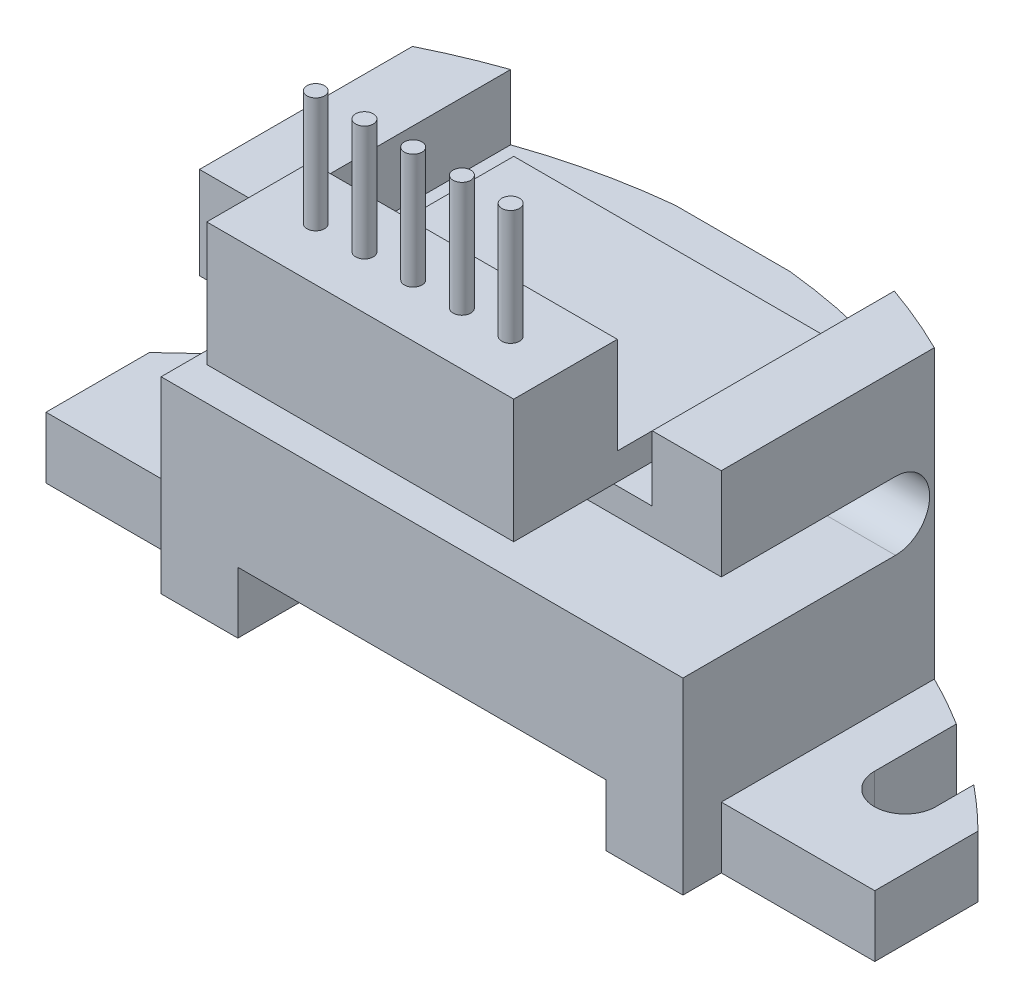
SolidWorks part; units mm, degrees
ref_plane "Front Plane" through (0, 0, 0) normal (0, 0, 1) x (1, 0, 0)
ref_plane "Top Plane" through (0, 0, 0) normal (0, 1, 0) x (1, 0, 0)
ref_plane "Right Plane" through (0, 0, 0) normal (1, 0, 0) x (0, 0, -1)
sketch "Sketch1" plane through (0, 0, 0) normal (0, 1, 0) x (1, 0, 0)
  line L0 (0, 0) -> (8.9, 0) construction
  line L1 (10.8, 0) -> (10.8, -2.69)
  line L2 (0, 0) -> (0, 4.4) construction
  line L3 (0, 4.4) -> (1.5, 4.4) construction
  line L4 (0, -2.69) -> (6.8, -2.69) construction
  line L5 (6.8, -2.69) -> (10.8, -2.69)
  line L6 (6.8, -2.69) -> (6.8, 2.861)
  line L7 (8.1, 0) -> (8.1, 2.1345)
  line L8 (9.7, 0) -> (9.7, 0.9893)
  arc A0 (1.5, 4.4) -> (8.1, 2.1345) centre (-0.1031, -11.0169) cw construction
  circle A1 centre (8.9, 0) radius 0.8 construction
  arc A2 (9.7, 0.9893) -> (10.8, 0) centre (-0.1031, -11.0169) cw
  arc A3 (8.1, 2.1345) -> (6.8, 2.861) centre (-0.1031, -11.0169) ccw
  arc A4 (9.7, 0) -> (8.1, 0) centre (8.9, 0) cw
  dimension "D7" = 15.5
  dimension "D8" = 1.6
  dimension "D1" = 8.9
  dimension "D2" = 10.8
  dimension "D3" = 2.69
  dimension "D4" = 4.4
  dimension "D5" = 1.5
  dimension "D6" = 6.8
extrude "Boss-Extrude1" add sketch "Sketch1" along normal blind 1.6 contours L8 A4 L7 A3 L6 L5 L1 A2
sketch "Sketch2" plane through (0, 1.6, 0) normal (0, 1, 0) x (1, 0, 0)
  line L0 (6.8, -2.69) -> (6.8, 2.861) construction
  line L1 (6.8, -2.69) -> (6.8, 2.861)
  line L2 (6.8, -2.69) -> (4.8, -2.69)
  line L3 (0, -2.69) -> (6.8, -2.69) construction
  line L4 (4.8, -2.69) -> (4.8, 3.6872)
  arc A0 (8.1, 2.1345) -> (1.5, 4.4) centre (-0.1031, -11.0169) ccw construction
  arc A1 (4.8, 3.6872) -> (6.8, 2.861) centre (-0.1031, -11.0169) cw
  dimension "D1" = 2
extrude "Boss-Extrude2" add sketch "Sketch2" against normal blind 1.6
sketch "Sketch3" plane through (0, 1.6, 0) normal (0, 1, 0) x (1, 0, 0)
  line L0 (6.8, -2.69) -> (6.8, 2.861) construction
  line L1 (6.8, -2.69) -> (6.8, 2.861)
  line L2 (0, -2.69) -> (6.8, -2.69)
  line L3 (1.5, 4.4) -> (1.5, 1.9)
  line L4 (1.5, 1.9) -> (0, 1.9)
  line L5 (0, 0) -> (0, 4.4) construction
  line L6 (0, 1.9) -> (0, -2.69) construction
  line L7 (0, 1.9) -> (0, -2.69)
  arc A0 (8.1, 2.1345) -> (1.5, 4.4) centre (-0.1031, -11.0169) ccw construction
  arc A1 (6.8, 2.861) -> (1.5, 4.4) centre (-0.1031, -11.0169) ccw
  dimension "D1" = 2.5
extrude "Boss-Extrude3" add sketch "Sketch3" along normal blind 3.3
sketch "Sketch4" plane through (0, 0, 2.69) normal (0, 0, 1) x (1, 0, 0)
  line L0 (6.8, 1.6) -> (6.8, 0)
  line L1 (8.1, 0) -> (6.8, 0) construction
  line L2 (8.1, 0) -> (1.5, 0) construction
  line L3 (6.8, 4.9) -> (6.8, 1.6) construction
  line L4 (4.8, 0) -> (4.8, 1.6) construction
  line L5 (6.8, 4.9) -> (6.8, 1.6)
  line L6 (4.8, 0) -> (4.8, 1.6)
  line L7 (4.8, 0) -> (6.8, 0)
  line L12 (0, 4.9) -> (6.8, 4.9)
  line L13 (0, 4.9) -> (0, 1.6) construction
  line L14 (0, 4.9) -> (6.8, 4.9) construction
  line L15 (0, 4.9) -> (0, 1.6)
  line L16 (0, 1.6) -> (4.8, 1.6)
extrude "Boss-Extrude4" add sketch "Sketch4" along normal blind 1
sketch "Sketch5" plane through (0, 0, 0) normal (-1, 0, 0) x (0, 0, 1)
  line L0 (0, 0) -> (0, 4.9) construction
  line L1 (-1.9, 4.9) -> (3.69, 4.9) construction
  line L2 (0, 4.9) -> (0, 6.68) construction
  line L3 (0, 6.68) -> (11, 6.68) construction
  line L4 (11, 6.18) -> (-1.85, 6.18) construction
  line L5 (0, 5.79) -> (-1.85, 5.79) construction
  line L6 (-4.4, 4.9) -> (-1.9, 4.9) construction
  line L7 (-1.85, 5.79) -> (-1.85, 4.9) construction
  line L8 (-2.861, 4.9) -> (-1.85, 4.9)
  line L9 (2.69, 0) -> (2.69, 1.6) construction
  line L10 (2.69, 0) -> (2.69, 1.6) construction
  line L11 (-1.85, 6.68) -> (2.69, 6.68)
  line L12 (2.69, 6.68) -> (2.69, 9.08)
  line L13 (2.69, 9.08) -> (-2.861, 9.08)
  line L14 (-2.861, 4.9) -> (-2.861, 1.6) construction
  line L15 (-2.861, 4.9) -> (-2.861, 1.6) construction
  line L16 (-2.861, 9.08) -> (-2.861, 4.9)
  circle A0 centre (-1.85, 5.79) radius 0.89 construction
  arc A1 (-1.85, 4.9) -> (-1.85, 6.68) centre (-1.85, 5.79) cw
  dimension "D1" = 1.78
  dimension "D2" = 11
  dimension "D3" = 0.5
  dimension "D4" = 12.85
  dimension "D5" = 2.4
sketch "Sketch6" plane through (6.8, 0, 0) normal (1, 0, 0) x (0, 0, -1)
  line L0 (-2.69, 9.08) -> (2.861, 9.08) construction
  line L1 (-2.69, 6.68) -> (-2.69, 9.08) construction
  line L2 (1.85, 6.68) -> (-2.69, 6.68) construction
  line L3 (2.861, 4.9) -> (1.85, 4.9) construction
  line L4 (2.861, 9.08) -> (2.861, 4.9) construction
  line L5 (-2.69, 9.08) -> (2.861, 9.08)
  line L6 (-2.69, 6.68) -> (-2.69, 9.08)
  line L7 (1.85, 6.68) -> (-2.69, 6.68)
  line L8 (2.861, 4.9) -> (1.85, 4.9)
  line L9 (2.861, 9.08) -> (2.861, 4.9)
  arc A0 (1.85, 4.9) -> (1.85, 6.68) centre (1.85, 5.79) ccw construction
  arc A1 (1.85, 4.9) -> (1.85, 6.68) centre (1.85, 5.79) ccw
extrude "Boss-Extrude5" add sketch "Sketch6" against normal up to surface (6.8 mm away) up to face at (0, 3.25, 0.895)
sketch "Sketch7" plane through (0, 4.9, 0) normal (0, 1, 0) x (1, 0, 0)
  line L0 (0, 2.861) -> (6.8, 2.861) construction
  line L1 (0, 4.4) -> (1.5, 4.4) construction
  line L2 (0, 2.861) -> (6.8, 2.861)
  line L3 (0, 4.4) -> (1.5, 4.4)
  line L4 (0, 4.4) -> (0, 2.861)
  arc A0 (8.1, 2.1345) -> (1.5, 4.4) centre (-0.1031, -11.0169) ccw construction
  arc A1 (8.1, 2.1345) -> (1.5, 4.4) centre (-0.1031, -11.0169) ccw
  line M1 (1.5, 2.861) -> (6.8, 2.861)
  arc M2 (6.8, 2.861) -> (1.5, 4.4) centre (-0.1031, -11.0169) ccw
  line M3 (1.5, 4.4) -> (1.5, 2.861)
extrude "Boss-Extrude6" add sketch "Sketch7" along normal up to surface (4.18 mm away) contours L3 L4 L2 M3 | M3 M1 M2 up to face at (3.4, 9.08, -0.0855)
sketch "Sketch8" plane through (0, 0, 0) normal (0, -1, 0) x (1, 0, 0)
  circle A0 centre (6.3, 0) radius 1
  dimension "D2" = 2
  dimension "D1" = 6.3
extrude "Boss-Extrude7" add sketch "Sketch8" along normal blind 0.8
sketch "Sketch9" plane through (0, 0, 2.69) normal (0, 0, 1) x (1, 0, 0)
  line L1 (0, 9.08) -> (5, 9.08)
  line L2 (0, 9.08) -> (0, 7.38)
  line L3 (0, 7.38) -> (5, 7.38)
  line L4 (5, 9.08) -> (5, 7.38)
  dimension "D1" = 5
  dimension "D2" = 1.7
extrude "Cut-Extrude1" cut sketch "Sketch9" against normal through all
mirror "Mirror3" about plane through (0, 4.9, -1.9) normal (1, 0, 0) of bodies 110
sketch "Sketch10" plane through (0, 0, 0) normal (1, 0, 0) x (0, 0, -1)
  line L0 (0, 0) -> (0, 7.38) construction
  line L1 (-1, 0) -> (1, 0) construction
  line L3 (3.619, 7.38) -> (-2.69, 7.38) construction
  line L4 (3.619, 7.38) -> (-2.69, 7.38) construction
  line L5 (0, 7.38) -> (-5.3, 7.38)
  line L6 (-5.3, 7.38) -> (-5.3, 10.6)
  line L7 (-5.3, 10.6) -> (-2.6, 10.6)
  line L8 (-2.6, 10.6) -> (-2.6, 8.08)
  line L9 (-2.6, 8.08) -> (0, 8.08)
  line L10 (0, 8.08) -> (0, 7.38) construction
  line L11 (0, 8.08) -> (2.7, 8.08)
  line L12 (2.7, 8.08) -> (2.7, 7.38)
  line L13 (2.7, 7.38) -> (0, 7.38)
  line L14 (2.861, 9.08) -> (-2.69, 9.08) construction
  dimension "D1" = 5.3
  dimension "D2" = 1.52
  dimension "D3" = 0.7
  dimension "D4" = 2.7
  dimension "D5" = 2.7
extrude "Boss-Extrude8" add sketch "Sketch10" along normal mid plane 8
sketch "Sketch11" plane through (0, 0, 0) normal (1, 0, 0) x (0, 0, -1)
  line L0 (-3.69, 10.6) -> (-3.69, 11.9743) construction
  line L1 (-2.6, 10.6) -> (-5.3, 10.6) construction
  line L2 (-3.69, 0) -> (-3.69, 4.9) construction
sketch "Sketch12" plane through (0, 10.6, 0) normal (0, 1, 0) x (1, 0, 0)
  circle A0 centre (0, -3.92) radius 0.23
  circle A1 centre (1.27, -3.92) radius 0.23
  circle A2 centre (2.54, -3.92) radius 0.23
  circle A3 centre (-1.27, -3.92) radius 0.23
  circle A4 centre (-2.54, -3.92) radius 0.23
  dimension "D2" = 0.46
  dimension "D1" = 3.92
  dimension "D5" = 1.27
  dimension "D6" = 1.27
  dimension "D3" = 3
  dimension "D4" = 3
extrude "Boss-Extrude9" add sketch "Sketch12" along normal blind 3
